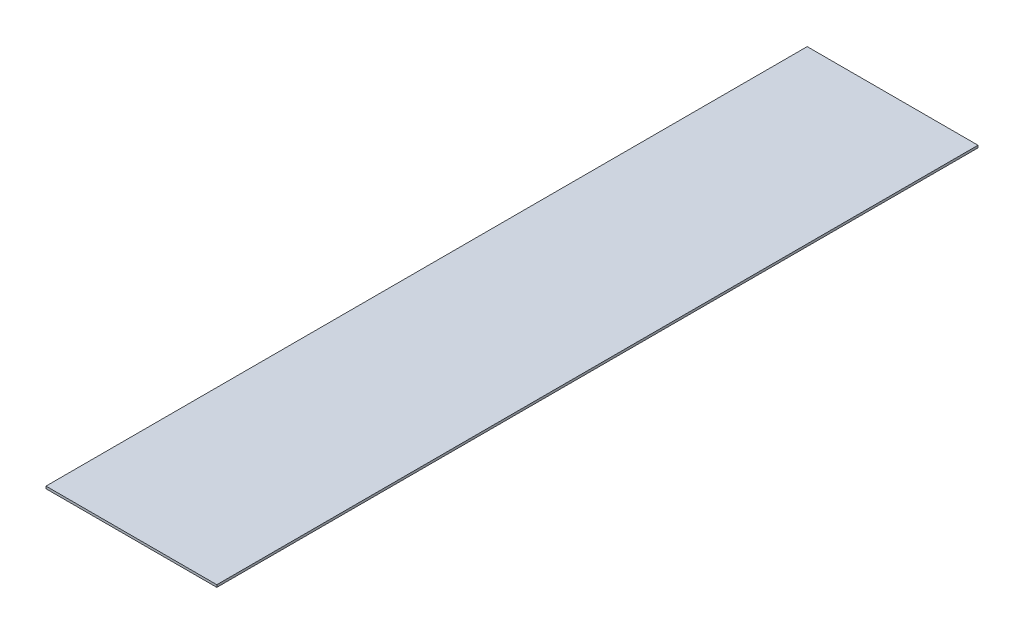
SolidWorks part; units mm, degrees
ref_plane "Front Plane" through (0, 0, 0) normal (0, 0, 1) x (1, 0, 0)
ref_plane "Top Plane" through (0, 0, 0) normal (0, 1, 0) x (1, 0, 0)
ref_plane "Right Plane" through (0, 0, 0) normal (1, 0, 0) x (0, 0, -1)
sketch "Sketch1" plane through (0, 0, 0) normal (0, 1, 0) x (1, 0, 0)
  line L1 (-365.8573, 330.9159) -> (-180.4373, 330.9159)
  line L2 (-365.8573, 330.9159) -> (-365.8573, -495.3461)
  line L3 (-365.8573, -495.3461) -> (-180.4373, -495.3461)
  line L4 (-180.4373, 330.9159) -> (-180.4373, -495.3461)
  dimension "D1" = 826.262
  dimension "D2" = 185.42
extrude "Boss-Extrude1" add sketch "Sketch1" along normal blind 2.54
